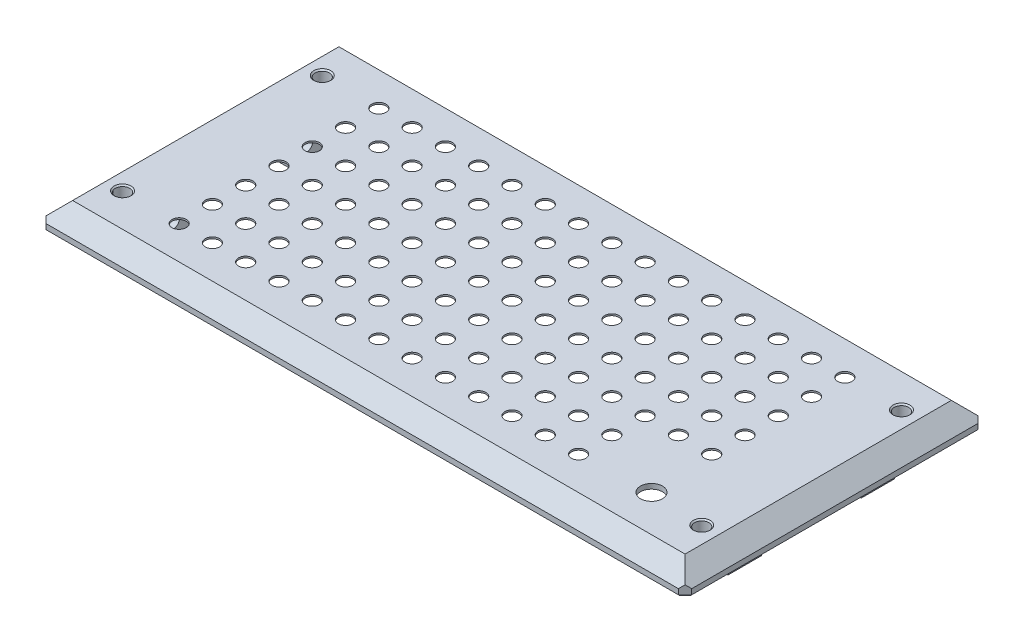
SolidWorks part; units mm, degrees
ref_plane "Front Plane" through (0, 0, 0) normal (0, 0, 1) x (1, 0, 0)
ref_plane "Top Plane" through (0, 0, 0) normal (0, 1, 0) x (1, 0, 0)
ref_plane "Right Plane" through (0, 0, 0) normal (1, 0, 0) x (0, 0, -1)
sketch "Sketch1" plane through (0, 0, 0) normal (0, 1, 0) x (1, 0, 0)
  line L1 (-97, -45) -> (97, -45)
  line L2 (-97, -45) -> (-97, 45)
  line L3 (-97, 45) -> (97, 45)
  line L4 (97, -45) -> (97, 45)
  line L5 (-97, -45) -> (97, 45) construction
  line L6 (-97, 45) -> (97, -45) construction
  point P0 (0, 0)
  dimension "D1" = 194
  dimension "D2" = 90
extrude "Boss-Extrude1" add sketch "Sketch1" along normal blind 2
sketch "Sketch2" plane through (0, 2, 0) normal (0, 1, 0) x (1, 0, 0)
  line L4 (97, -45) -> (97, 45)
  line L5 (97, 45) -> (-97, 45)
  line L6 (-97, 45) -> (-97, -45)
  line L7 (-97, -45) -> (97, -45)
  line L8 (97, -45) -> (97, 45)
  line L9 (97, 45) -> (-97, 45)
  line L10 (-97, 45) -> (-97, -45)
  line L11 (-97, -45) -> (97, -45)
  dimension "D1" = 0
ref_plane "Plane1" through (0, 7, 0) normal (0, 1, 0) x (1, 0, 0)
sketch "Sketch3" plane through (0, 7, 0) normal (0, 1, 0) x (1, 0, 0)
  line L0 (-97, 45) -> (-97, -45) construction
  line L1 (-92, -40) -> (92, -40)
  line L2 (-92, -40) -> (-92, 40)
  line L3 (-92, 40) -> (92, 40)
  line L4 (92, -40) -> (92, 40)
  line L5 (-92, -40) -> (92, 40) construction
  line L6 (-92, 40) -> (92, -40) construction
  line L7 (97, 45) -> (-97, 45) construction
  point P0 (0, 0)
  dimension "D1" = 5
  dimension "D2" = 5
loft "Loft1" add profiles "Sketch3", "Sketch2"
chamfer "Chamfer2" distance 2 angle 45 4 edges at (97, 1, 45) (97, 1, -45) (-97, 1, -45) (-97, 1, 45)
sketch "Sketch4" plane through (0, 0, 0) normal (0, -1, 0) x (1, 0, 0)
  line L0 (-97, -43) -> (-97, 43) construction
  line L1 (-89.9, 15) -> (-81.9, 15)
  line L2 (-89.9, 15) -> (-89.9, 25)
  line L3 (-89.9, 25) -> (-81.9, 25)
  line L4 (-81.9, 15) -> (-81.9, 25)
  line L5 (-89.9, 15) -> (-81.9, 25) construction
  line L6 (-89.9, 25) -> (-81.9, 15) construction
  line L7 (-97, 0) -> (97, 0) construction
  line L8 (97, 43) -> (97, -43) construction
  line L9 (0, 45) -> (0, -45) construction
  line L10 (-95, 45) -> (95, 45) construction
  line L11 (95, -45) -> (-95, -45) construction
  line L12 (-89.9, -25) -> (-81.9, -15) construction
  line L13 (-89.9, -15) -> (-81.9, -25) construction
  line L14 (-81.9, -15) -> (-81.9, -25)
  line L15 (-89.9, -25) -> (-81.9, -25)
  line L16 (-89.9, -15) -> (-89.9, -25)
  line L17 (-89.9, -15) -> (-81.9, -15)
  line L18 (89.9, -15) -> (81.9, -25) construction
  line L19 (89.9, -25) -> (81.9, -15) construction
  line L20 (89.9, 25) -> (81.9, 15) construction
  line L21 (89.9, 15) -> (81.9, 25) construction
  line L22 (89.9, -15) -> (81.9, -15)
  line L23 (89.9, -15) -> (89.9, -25)
  line L24 (89.9, -25) -> (81.9, -25)
  line L25 (81.9, -15) -> (81.9, -25)
  line L26 (81.9, 15) -> (81.9, 25)
  line L27 (89.9, 25) -> (81.9, 25)
  line L28 (89.9, 15) -> (89.9, 25)
  line L29 (89.9, 15) -> (81.9, 15)
  point P0 (-85.9, 20)
  point P21 (-85.9, -20)
  point P30 (85.9, -20)
  point P31 (85.9, 20)
  dimension "D1" = 10
  dimension "D2" = 7.1
  dimension "D3" = 8
  dimension "D4" = 40
extrude "Boss-Extrude2" add sketch "Sketch4" along normal blind 7
sketch "Sketch5" plane through (-89.9, 0, 0) normal (-1, 0, 0) x (0, 0, 1)
  line L0 (-15, 0) -> (-25, -7) construction
  line L1 (0, 0) -> (0, 50000) construction
  circle A0 centre (-20, -3.5) radius 2.05
  circle A1 centre (20, -3.5) radius 2.05
  dimension "D1" = 4.1
extrude "Cut-Extrude1" cut sketch "Sketch5" against normal through all
sketch "Sketch6" plane through (0, 0, 0) normal (0, -1, 0) x (1, 0, 0)
  line L0 (81.9, 25) -> (81.9, 15) construction
  line L1 (-80.9, -39) -> (80.9, -39)
  line L2 (-80.9, -39) -> (-80.9, 39)
  line L3 (-80.9, 39) -> (80.9, 39)
  line L4 (80.9, -39) -> (80.9, 39)
  line L5 (-80.9, -39) -> (80.9, 39) construction
  line L6 (-80.9, 39) -> (80.9, -39) construction
  line L8 (-92, 40) -> (92, 40) construction
  point P0 (0, 0)
  dimension "D1" = 1
  dimension "D2" = 1
extrude "Cut-Extrude2" cut sketch "Sketch6" against normal offset from surface (5.5 mm away) 1.5 up to face at (0, 7, 0)
sketch "Sketch7" plane through (0, 5.5, 0) normal (0, -1, 0) x (1, 0, 0)
  line L0 (0, 39) -> (0, -39) construction
  line L1 (-80.9, 39) -> (80.9, 39) construction
  line L2 (-80.9, -39) -> (80.9, -39) construction
  line L3 (-80.9, 0) -> (80.9, 0) construction
  line L4 (-80.9, -39) -> (-80.9, 39) construction
  line L5 (80.9, 39) -> (80.9, -39) construction
  circle A0 centre (0, 0) radius 2.15
  circle A1 centre (10, 0) radius 2.15
  circle A2 centre (20, 0) radius 2.15
  circle A3 centre (30, 0) radius 2.15
  circle A4 centre (40, 0) radius 2.15
  circle A5 centre (50, 0) radius 2.15
  circle A7 centre (10, 10) radius 2.15
  circle A8 centre (20, 10) radius 2.15
  circle A9 centre (30, 10) radius 2.15
  circle A10 centre (40, 10) radius 2.15
  circle A11 centre (50, 10) radius 2.15
  circle A13 centre (10, 20) radius 2.15
  circle A14 centre (20, 20) radius 2.15
  circle A15 centre (30, 20) radius 2.15
  circle A16 centre (40, 20) radius 2.15
  circle A17 centre (50, 20) radius 2.15
  circle A19 centre (10, 30) radius 2.15
  circle A20 centre (20, 30) radius 2.15
  circle A21 centre (30, 30) radius 2.15
  circle A22 centre (40, 30) radius 2.15
  circle A23 centre (50, 30) radius 2.15
  circle A25 centre (0, 10) radius 2.15
  circle A26 centre (0, 20) radius 2.15
  circle A27 centre (0, 30) radius 2.15
  circle A35 centre (-50, 30) radius 2.15
  circle A36 centre (-40, 30) radius 2.15
  circle A37 centre (-30, 30) radius 2.15
  circle A38 centre (-20, 30) radius 2.15
  circle A39 centre (-10, 30) radius 2.15
  circle A40 centre (-50, 20) radius 2.15
  circle A41 centre (-40, 20) radius 2.15
  circle A42 centre (-30, 20) radius 2.15
  circle A43 centre (-20, 20) radius 2.15
  circle A44 centre (-10, 20) radius 2.15
  circle A45 centre (-50, 10) radius 2.15
  circle A46 centre (-40, 10) radius 2.15
  circle A47 centre (-30, 10) radius 2.15
  circle A48 centre (-20, 10) radius 2.15
  circle A49 centre (-10, 10) radius 2.15
  circle A50 centre (-50, 0) radius 2.15
  circle A51 centre (-40, 0) radius 2.15
  circle A52 centre (-30, 0) radius 2.15
  circle A53 centre (-20, 0) radius 2.15
  circle A54 centre (-10, 0) radius 2.15
  circle A55 centre (-10, -10) radius 2.15
  circle A56 centre (-20, -10) radius 2.15
  circle A57 centre (-30, -10) radius 2.15
  circle A58 centre (-40, -10) radius 2.15
  circle A59 centre (-50, -10) radius 2.15
  circle A60 centre (-10, -20) radius 2.15
  circle A61 centre (-20, -20) radius 2.15
  circle A62 centre (-30, -20) radius 2.15
  circle A63 centre (-40, -20) radius 2.15
  circle A64 centre (-50, -20) radius 2.15
  circle A65 centre (-10, -30) radius 2.15
  circle A66 centre (-20, -30) radius 2.15
  circle A67 centre (-30, -30) radius 2.15
  circle A68 centre (-40, -30) radius 2.15
  circle A69 centre (-50, -30) radius 2.15
  circle A70 centre (0, -30) radius 2.15
  circle A71 centre (0, -20) radius 2.15
  circle A72 centre (0, -10) radius 2.15
  circle A73 centre (50, -30) radius 2.15
  circle A74 centre (40, -30) radius 2.15
  circle A75 centre (30, -30) radius 2.15
  circle A76 centre (20, -30) radius 2.15
  circle A77 centre (10, -30) radius 2.15
  circle A78 centre (50, -20) radius 2.15
  circle A79 centre (40, -20) radius 2.15
  circle A80 centre (30, -20) radius 2.15
  circle A81 centre (20, -20) radius 2.15
  circle A82 centre (10, -20) radius 2.15
  circle A83 centre (50, -10) radius 2.15
  circle A84 centre (40, -10) radius 2.15
  circle A85 centre (30, -10) radius 2.15
  circle A86 centre (20, -10) radius 2.15
  circle A87 centre (10, -10) radius 2.15
  circle A88 centre (60, 0) radius 2.15
  circle A89 centre (70, 0) radius 2.15
  circle A90 centre (60, 10) radius 2.15
  circle A91 centre (70, 10) radius 2.15
  circle A92 centre (60, 20) radius 2.15
  circle A93 centre (70, 20) radius 2.15
  circle A94 centre (60, 30) radius 2.15
  circle A95 centre (70, 30) radius 2.15
  circle A96 centre (70, -30) radius 2.15
  circle A97 centre (60, -30) radius 2.15
  circle A98 centre (70, -20) radius 2.15
  circle A99 centre (60, -20) radius 2.15
  circle A100 centre (70, -10) radius 2.15
  circle A101 centre (60, -10) radius 2.15
  circle A102 centre (-60, -10) radius 2.15
  circle A103 centre (-70, -10) radius 2.15
  circle A104 centre (-60, -20) radius 2.15
  circle A105 centre (-70, -20) radius 2.15
  circle A106 centre (-60, -30) radius 2.15
  circle A107 centre (-70, -30) radius 2.15
  circle A108 centre (-70, 30) radius 2.15
  circle A109 centre (-60, 30) radius 2.15
  circle A110 centre (-70, 20) radius 2.15
  circle A111 centre (-60, 20) radius 2.15
  circle A112 centre (-70, 10) radius 2.15
  circle A113 centre (-60, 10) radius 2.15
  circle A114 centre (-70, 0) radius 2.15
  circle A115 centre (-60, 0) radius 2.15
  dimension "D1" = 4.3
  dimension "D2" = 8
  dimension "D3" = 4
extrude "Cut-Extrude3" cut sketch "Sketch7" against normal through all
sketch "Sketch8" plane through (0, 5.5, 0) normal (0, -1, 0) x (1, 0, 0)
  line L0 (0, 39) -> (0, -39) construction
  line L1 (-80.9, 39) -> (80.9, 39) construction
  line L2 (80.9, -39) -> (-80.9, -39) construction
  line L3 (-80.9, 0) -> (80.9, 0) construction
  line L4 (-80.9, -39) -> (-80.9, 39) construction
  line L5 (80.9, -39) -> (80.9, 39) construction
  circle A0 centre (0, 0) radius 4.2
  circle A1 centre (10, 0) radius 4.2
  circle A2 centre (20, 0) radius 4.2
  circle A3 centre (30, 0) radius 4.2
  circle A4 centre (40, 0) radius 4.2
  circle A5 centre (50, 0) radius 4.2
  circle A6 centre (10, 10) radius 4.2
  circle A7 centre (20, 10) radius 4.2
  circle A8 centre (30, 10) radius 4.2
  circle A9 centre (40, 10) radius 4.2
  circle A10 centre (50, 10) radius 4.2
  circle A11 centre (10, 20) radius 4.2
  circle A12 centre (20, 20) radius 4.2
  circle A13 centre (30, 20) radius 4.2
  circle A14 centre (40, 20) radius 4.2
  circle A15 centre (50, 20) radius 4.2
  circle A16 centre (10, 30) radius 4.2
  circle A17 centre (20, 30) radius 4.2
  circle A18 centre (30, 30) radius 4.2
  circle A19 centre (40, 30) radius 4.2
  circle A20 centre (50, 30) radius 4.2
  circle A21 centre (0, 10) radius 4.2
  circle A22 centre (0, 20) radius 4.2
  circle A23 centre (0, 30) radius 4.2
  circle A24 centre (0, -30) radius 4.2
  circle A25 centre (0, -20) radius 4.2
  circle A26 centre (0, -10) radius 4.2
  circle A27 centre (50, -30) radius 4.2
  circle A28 centre (40, -30) radius 4.2
  circle A29 centre (30, -30) radius 4.2
  circle A30 centre (20, -30) radius 4.2
  circle A31 centre (10, -30) radius 4.2
  circle A32 centre (50, -20) radius 4.2
  circle A33 centre (40, -20) radius 4.2
  circle A34 centre (30, -20) radius 4.2
  circle A35 centre (20, -20) radius 4.2
  circle A36 centre (10, -20) radius 4.2
  circle A37 centre (50, -10) radius 4.2
  circle A38 centre (40, -10) radius 4.2
  circle A39 centre (30, -10) radius 4.2
  circle A40 centre (20, -10) radius 4.2
  circle A41 centre (10, -10) radius 4.2
  circle A42 centre (-10, -10) radius 4.2
  circle A43 centre (-20, -10) radius 4.2
  circle A44 centre (-30, -10) radius 4.2
  circle A45 centre (-40, -10) radius 4.2
  circle A46 centre (-50, -10) radius 4.2
  circle A47 centre (-10, -20) radius 4.2
  circle A48 centre (-20, -20) radius 4.2
  circle A49 centre (-30, -20) radius 4.2
  circle A50 centre (-40, -20) radius 4.2
  circle A51 centre (-50, -20) radius 4.2
  circle A52 centre (-10, -30) radius 4.2
  circle A53 centre (-20, -30) radius 4.2
  circle A54 centre (-30, -30) radius 4.2
  circle A55 centre (-40, -30) radius 4.2
  circle A56 centre (-50, -30) radius 4.2
  circle A57 centre (-50, 30) radius 4.2
  circle A58 centre (-40, 30) radius 4.2
  circle A59 centre (-30, 30) radius 4.2
  circle A60 centre (-20, 30) radius 4.2
  circle A61 centre (-10, 30) radius 4.2
  circle A62 centre (-50, 20) radius 4.2
  circle A63 centre (-40, 20) radius 4.2
  circle A64 centre (-30, 20) radius 4.2
  circle A65 centre (-20, 20) radius 4.2
  circle A66 centre (-10, 20) radius 4.2
  circle A67 centre (-50, 10) radius 4.2
  circle A68 centre (-40, 10) radius 4.2
  circle A69 centre (-30, 10) radius 4.2
  circle A70 centre (-20, 10) radius 4.2
  circle A71 centre (-10, 10) radius 4.2
  circle A72 centre (-50, 0) radius 4.2
  circle A73 centre (-40, 0) radius 4.2
  circle A74 centre (-30, 0) radius 4.2
  circle A75 centre (-20, 0) radius 4.2
  circle A76 centre (-10, 0) radius 4.2
  circle A77 centre (60, 0) radius 4.2
  circle A78 centre (70, 0) radius 4.2
  circle A81 centre (60, 10) radius 4.2
  circle A82 centre (70, 10) radius 4.2
  circle A85 centre (60, 20) radius 4.2
  circle A86 centre (70, 20) radius 4.2
  circle A89 centre (60, 30) radius 4.2
  circle A90 centre (70, 30) radius 4.2
  circle A93 centre (70, -30) radius 4.2
  circle A94 centre (60, -30) radius 4.2
  circle A95 centre (70, -20) radius 4.2
  circle A96 centre (60, -20) radius 4.2
  circle A97 centre (70, -10) radius 4.2
  circle A98 centre (60, -10) radius 4.2
  circle A99 centre (-60, -10) radius 4.2
  circle A100 centre (-60, -20) radius 4.2
  circle A101 centre (-60, -30) radius 4.2
  circle A102 centre (-60, 0) radius 4.2
  circle A103 centre (-70, -10) radius 4.2
  circle A104 centre (-70, -20) radius 4.2
  circle A105 centre (-70, -30) radius 4.2
  circle A106 centre (-70, 30) radius 4.2
  circle A107 centre (-60, 30) radius 4.2
  circle A108 centre (-70, 20) radius 4.2
  circle A109 centre (-60, 20) radius 4.2
  circle A110 centre (-70, 10) radius 4.2
  circle A111 centre (-60, 10) radius 4.2
  circle A112 centre (-70, 0) radius 4.2
  dimension "D1" = 8.4
  dimension "D2" = 8
  dimension "D3" = 4
extrude "Cut-Extrude4" cut sketch "Sketch8" against normal blind 1
sketch "Sketch9" plane through (0, 7, 0) normal (0, 1, 0) x (1, 0, 0)
  line L1 (80.9, -39) -> (61.6, -39)
  line L2 (80.9, -39) -> (80.9, -19.5)
  line L3 (80.9, -19.5) -> (61.6, -19.5)
  line L4 (61.6, -39) -> (61.6, -19.5)
  dimension "D1" = 19.3
  dimension "D2" = 19.5
sketch "Sketch13" plane through (0, 5.5, 0) normal (0, -1, 0) x (1, 0, 0)
  circle A8 centre (60, 20) radius 4.2 construction
  circle A9 centre (70, 20) radius 4.2 construction
  circle A10 centre (70, 30) radius 4.2 construction
  circle A11 centre (60, 30) radius 4.2 construction
  circle A12 centre (60, 20) radius 4.2
  circle A13 centre (70, 20) radius 4.2
  circle A14 centre (70, 30) radius 4.2
  circle A15 centre (60, 30) radius 4.2
extrude "Boss-Extrude3" add sketch "Sketch13" against normal up to surface (1.5 mm away) up to face at (-30, 7, -2.15)
sketch "Sketch10" plane through (0, 5.5, 0) normal (0, -1, 0) x (1, 0, 0)
  line L1 (80.9, 39) -> (70.9, 39) construction
  line L2 (80.9, 39) -> (80.9, 29) construction
  line L3 (80.9, 29) -> (70.9, 29) construction
  line L4 (70.9, 39) -> (70.9, 29) construction
  circle A0 centre (70.9, 29) radius 3.3
  dimension "D1" = 6.6
  dimension "D2" = 10
extrude "Cut-Extrude5" cut sketch "Sketch10" against normal through all
sketch "Sketch11" plane through (0, 0, 0) normal (0, -1, 0) x (1, 0, 0)
  line L0 (80.9, 39) -> (80.9, -39) construction
  line L1 (80.9, 10) -> (90.9, 10)
  line L2 (80.9, 10) -> (80.9, -10)
  line L3 (80.9, -10) -> (90.9, -10)
  line L4 (90.9, 10) -> (90.9, -10)
  line L5 (-80.9, 39) -> (-80.9, -39) construction
  line L6 (-80.9, 10) -> (-90.9, 10)
  line L7 (-80.9, 10) -> (-80.9, -10)
  line L8 (-80.9, -10) -> (-90.9, -10)
  line L9 (-90.9, 10) -> (-90.9, -10)
  line L10 (-97, -43) -> (-97, 43) construction
  point P12 (-90.9, 0)
  point P15 (-97, 0)
  point P16 (90.9, 0)
  dimension "D1" = 10
  dimension "D2" = 20
extrude "Cut-Extrude6" cut sketch "Sketch11" against normal up to surface (5.5 mm away) up to face at (70.9, 5.5, 25.7)
sketch "Sketch12" plane through (0, 0, 0) normal (0, -1, 0) x (1, 0, 0)
  line L0 (0, 0) -> (-87, 0) construction
  line L1 (-87, -30) -> (-87, 30) construction
  line L2 (-97, -43) -> (-97, 43) construction
  line L3 (0, 45) -> (0, -45) construction
  line L4 (-95, 45) -> (95, 45) construction
  line L5 (95, -45) -> (-95, -45) construction
  line L6 (87, -30) -> (87, 30) construction
  circle A0 centre (-87, 30) radius 2.15
  circle A1 centre (-87, -30) radius 2.15
  circle A2 centre (87, -30) radius 2.15
  circle A3 centre (87, 30) radius 2.15
  point P6 (-87, 0)
  point P20 (87, 0)
  dimension "D1" = 4.3
  dimension "D2" = 60
  dimension "D3" = 10
extrude "Cut-Extrude7" cut sketch "Sketch12" against normal through all
chamfer "Chamfer3" distance 0.4 angle 45 8 edges at (-96, 0, -44) (-97, 0, 0) (-96, 0, 44) (0, 0, 45) (96, 0, 44) (97, 0, 0) (96, 0, -44) (0, 0, -45)
chamfer "Chamfer4" distance 0.4 angle 45 4 edges at (87, 7, 27.85) (87, 7, -32.15) (-87, 7, 27.85) (-87, 7, -32.15)
chamfer "Chamfer5" distance 0.4 angle 45 4 edges at (-89.9, -3.5, 17.95) (-89.9, -3.5, -17.95) (89.9, -3.5, 22.05) (89.9, -3.5, -17.95)
